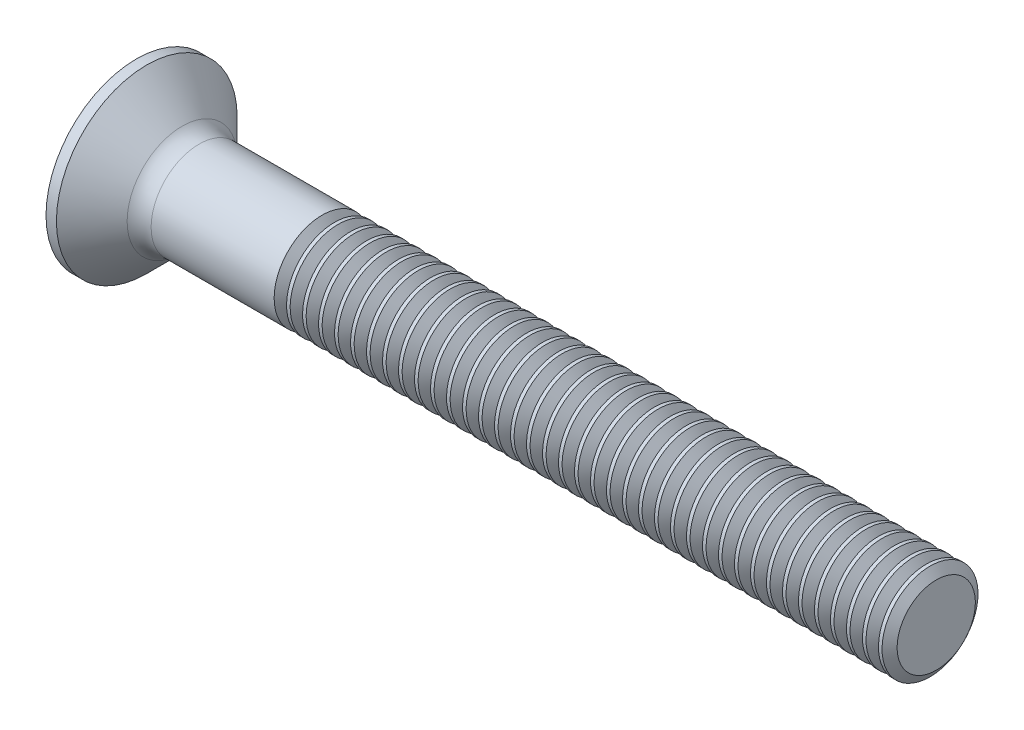
SolidWorks part; units mm, degrees
ref_plane "Plane1" through (0, 0, 0) normal (0, 0, 1) x (1, 0, 0)
ref_plane "Plane2" through (0, 0, 0) normal (0, 1, 0) x (1, 0, 0)
ref_plane "Plane3" through (0, 0, 0) normal (1, 0, 0) x (0, 0, -1)
sketch "BodySke" plane through (0, 0, 0) normal (0, 0, 1) x (1, 0, 0)
  line L0 (0, 0) -> (0, 5.65)
  line L1 (0, 5.65) -> (0.65, 5.65)
  line L2 (3.3, 3) -> (50, 3)
  line L3 (50, 3) -> (50, 0)
  line L4 (50, 0) -> (0, 0)
  line L5 (-6.35, 0) -> (82.55, 0) construction
  line L6 (3.3, -3) -> (50, -3) construction
  line L7 (0.65, -5.65) -> (3.3, -3) construction
  line L8 (0.65, 5.65) -> (3.3, 3)
  line L9 (0, -5.65) -> (0.65, -5.65) construction
  line L10 (4.3, 4.5875) -> (4.3, -4.9375) construction
  line L11 (12, 6.35) -> (12, -3.175) construction
  dimension "Diameter" = 6
  dimension "Length" = 50
  dimension "Head_ht" = 3.3
  dimension "Head_dia" = 11.3
  dimension "Head_ang" = 90
  dimension "D6" = 0.65
  dimension "Advance" = 1
  dimension "Thread_nom" = 38
revolve "Base-Revolve" add sketch "BodySke" angle 360 about L5
cosmetic thread "ThreadCosmetic" [suppressed] parameters "Thread_length"=13.5, "Thread_minor"=4.891
fillet "Fillet1" radius 1.5 1 edges at (3.3, 0, 3)
sketch "Sketch3" plane through (0, 0, 0) normal (-1, 0, 0) x (0, 0, 1)
  line L0 (-0.71, 3.3) -> (0.71, 3.3)
  line L1 (0.71, 3.3) -> (0.71, -3.3)
  line L2 (0.71, -3.3) -> (-0.71, -3.3)
  line L3 (-0.71, -3.3) -> (-0.71, 3.3)
  dimension "D1" = 4.9
  dimension "Cross_dia" = 6.6
  dimension "D2" = 1.08
  dimension "Cross_width" = 1.42
ref_plane "Plane4" through (3.45, 0, 0) normal (-1, 0, 0) x (0, 0, 1)
sketch "Sketch4" plane through (3.45, 0, 0) normal (-1, 0, 0) x (0, 0, 1)
  line L0 (-0.71, 1.5799) -> (0.71, 1.5799)
  line L3 (0.71, 1.5799) -> (0.71, -1.5799)
  line L4 (0.71, -1.5799) -> (-0.71, -1.5799)
  line L5 (-0.71, -1.5799) -> (-0.71, 1.5799)
  dimension "D1" = 2.16
  dimension "D2" = 4.176
  dimension "D3" = 1.08
  dimension "D4" = 2.088
loft "Recess" cut profiles "Sketch3", "Sketch4"
pattern_circular "RecPat" count 2 every 90 about axis through (0, 0, 0) along (1, 0, 0) of "Recess"
sketch "RecCorSke" plane through (0, 0, 0) normal (0, 0, 1) x (1, 0, 0)
  line L0 (-3.175, 0) -> (15.875, 0) construction
  line L2 (0, 0) -> (0, 1.5217)
  line L3 (0, 1.5217) -> (3.45, 1.2805)
  line L4 (3.45, 1.2805) -> (3.8661, 0)
  line L5 (3.8661, 0) -> (0, 0)
  dimension "Diameter" = 2.561
  dimension "Depth" = 5.64
  dimension "Draft_angle" = 4
  dimension "Bottom_angle" = 18
revolve "RecessCore" cut sketch "RecCorSke" angle 360 about L0
sketch "ThdSchSke" plane through (0, 0, 0) normal (0, 0, 1) x (1, 0, 0)
  line L0 (12, -2.4455) -> (11.6117, -3)
  line L1 (12, -2.4455) -> (12.3883, -3)
  line L2 (12.3883, -3) -> (12.3883, -3.75)
  line L3 (-3.175, 0) -> (5.1513, 0) construction
  line L5 (12.3883, -3.75) -> (11.6117, -3.75)
  line L6 (11.6117, -3.75) -> (11.6117, -3)
  line L7 (0, 5.65) -> (0, -5.65) construction
  dimension "Thread_minor" = 8.344
  dimension "Diameter" = 10
  dimension "Start" = 6.5
  dimension "SideAngle" = 55
  dimension "VeeAngle" = 70
  dimension "Overcut" = 12.5
revolve "ThreadSchematic" cut sketch "ThdSchSke" angle 360 about L3
pattern_linear "ThdSchPat" count 39 spacing 1 along (1, 0, 0) of "ThreadSchematic"
equation "\"D1@Sketch3\" = \"Cross_dia@Sketch3\" / 2"
equation "\"D2@Sketch3\" = \"Cross_width@Sketch3\" / 2"
equation "\"Depth@RecCorSke\" = \"Cross_depth@Plane4\""
equation "\"D1@Sketch4\" = \"Cross_width@Sketch3\""
equation "\"D2@Sketch4\" = \"Cross_dia@Sketch3\" - 2.0 * \"Cross_depth@Plane4\" * tan(26.5  * 0.017453292)"
equation "\"D3@Sketch4\" = \"D1@Sketch4\" / 2"
equation "\"D4@Sketch4\" = \"D2@Sketch4\" / 2"
equation "\"Thread_length@ThreadCosmetic\" = ((sgn( (\"Length@BodySke\" - \"Advance@BodySke\" * 1.0 - \"Head_ht@BodySke\" ) - \"Thread_nom@BodySke\" )-1)*( (\"Length@BodySke\" - \"Advance@BodySke\" * 1.0 - \"Head_ht@BodySke\" ) - \"Thread_nom@BodySke\" ))/-2+ \"Thread_nom@BodySke\""
equation "\"Thread_minor@ThdSchSke\" = \"Thread_minor@ThreadCosmetic\""
equation "\"Diameter@ThdSchSke\" = \"Diameter@BodySke\""
equation "\"Overcut@ThdSchSke\" = \"Diameter@BodySke\" * 1.25"
equation "\"Start@ThdSchSke\" = 0.000001 + \"Length@BodySke\" - \"Thread_length@ThreadCosmetic\"  '---Countersunk---"
equation "\"Num_threads@ThdSchPat\" = int( \"Thread_length@ThreadCosmetic\" / \"Advance@BodySke\" + 0.999 )  + 1"
equation "\"Advance@ThdSchPat\" = \"Thread_length@ThreadCosmetic\" /  (\"Num_threads@ThdSchPat\" - 1) 'relax it"
